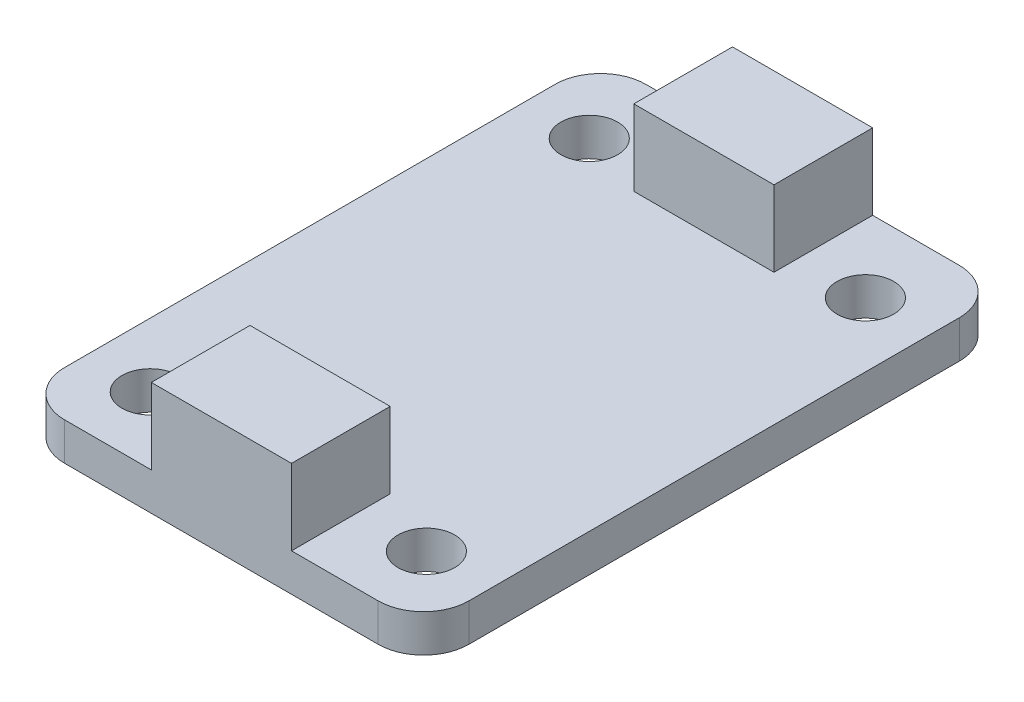
SolidWorks part; units mm, degrees
ref_plane "Front Plane" through (0, 0, 0) normal (0, 0, 1) x (1, 0, 0)
ref_plane "Top Plane" through (0, 0, 0) normal (0, 1, 0) x (1, 0, 0)
ref_plane "Right Plane" through (0, 0, 0) normal (1, 0, 0) x (0, 0, -1)
sketch "Sketch1" plane through (0, 0, 0) normal (0, 1, 0) x (1, 0, 0)
  line L1 (-10.397, 12.2204) -> (7.423, 12.2204)
  line L2 (-10.397, 12.2204) -> (-10.397, -13.3996)
  line L3 (-10.397, -13.3996) -> (7.423, -13.3996)
  line L4 (7.423, 12.2204) -> (7.423, -13.3996)
  dimension "D1" = 25.62
  dimension "D2" = 17.82
extrude "Boss-Extrude1" add sketch "Sketch1" along normal blind 1.66
sketch "Sketch2" plane through (0, 0, 0) normal (0, -1, 0) x (-1, 0, 0)
  line L0 (10.397, -13.3996) -> (-7.423, -13.3996) construction
  line L1 (4.577, -13.3996) -> (-1.603, -13.3996)
  line L2 (4.577, -13.3996) -> (4.577, -9.0496)
  line L3 (4.577, -9.0496) -> (-1.603, -9.0496)
  line L4 (-1.603, -13.3996) -> (-1.603, -9.0496)
  line L5 (10.397, -13.3996) -> (-7.423, -13.3996) construction
  line L6 (10.397, -0.5896) -> (-7.423, -0.5896) construction
  line L7 (10.397, 12.2204) -> (10.397, -13.3996) construction
  line L8 (-7.423, -13.3996) -> (-7.423, 12.2204) construction
  line L9 (-1.603, 12.2204) -> (-1.603, 7.8704)
  line L10 (4.577, 7.8704) -> (-1.603, 7.8704)
  line L11 (4.577, 12.2204) -> (4.577, 7.8704)
  line L12 (4.577, 12.2204) -> (-1.603, 12.2204)
  point P6 (1.487, -13.3996)
  point P9 (1.487, -13.3996)
  dimension "D1" = 6.18
  dimension "D2" = 4.35
extrude "Boss-Extrude2" add sketch "Sketch2" against normal blind 5
fillet "Fillet1" radius 2 4 edges at (-10.397, 0.83, 13.3996) (7.423, 0.83, 13.3996) (7.423, 0.83, -12.2204) (-10.397, 0.83, -12.2204)
hole_wizard "Hole1" positions "Sketch3" profile "Sketch4" legacy end condition through all
sketch "Sketch3" plane through (0, 1.66, 0) normal (0, 1, 0) x (1, 0, 0)
  point P0 (4.5917, -10.4436)
  point P2 (-7.58, -10.4436)
  point P4 (-7.58, 8.9096)
  point P6 (4.5917, 8.9096)
sketch "Sketch4" plane through (4.5917, 1.66, 10.4436) normal (1, 0, 0) x (0, 0, 1)
  line L0 (0, 0) -> (0, 1.66)
  line L1 (0, 1.66) -> (1.25, 1.66)
  line L2 (1.25, 1.66) -> (1.25, 0)
  line L3 (1.25, 0) -> (0, 0)
  line L4 (0, 110) -> (0, -10) construction
  dimension "Diameter" = 2.5
  dimension "Depth" = 1.66
